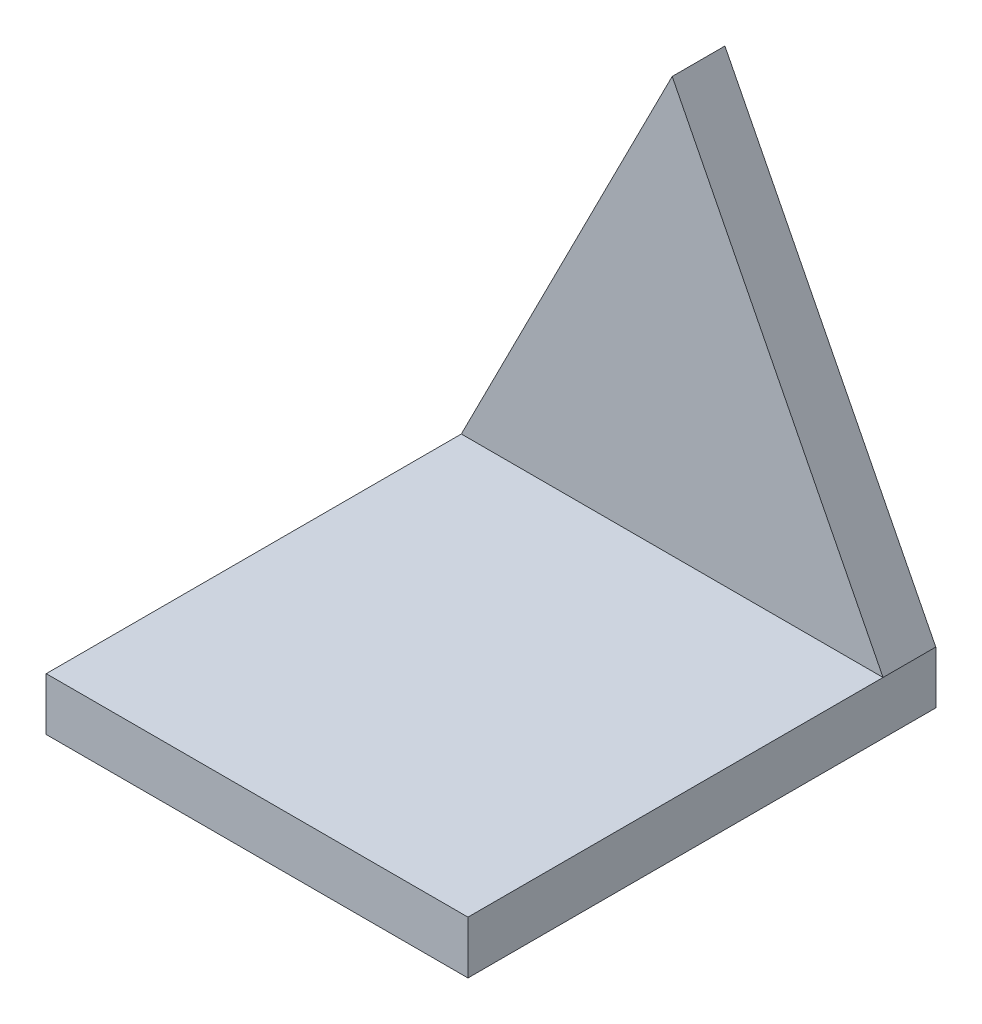
SolidWorks part; units mm, degrees
ref_plane "Front Plane" through (0, 0, 0) normal (0, 0, 1) x (1, 0, 0)
ref_plane "Top Plane" through (0, 0, 0) normal (0, 1, 0) x (1, 0, 0)
ref_plane "Right Plane" through (0, 0, 0) normal (1, 0, 0) x (0, 0, -1)
sketch "Sketch2" plane through (0, 0, 0) normal (0, 1, 0) x (1, 0, 0)
  line L1 (0, 0) -> (25.4, 0)
  line L2 (0, 0) -> (0, 28.175)
  line L3 (0, 28.175) -> (25.4, 28.175)
  line L4 (25.4, 0) -> (25.4, 28.175)
  dimension "D1" = 28.175
  dimension "D2" = 25.4
extrude "Boss-Extrude1" add sketch "Sketch2" along normal blind 3.175
sketch "Sketch3" plane through (0, 3.175, 0) normal (0, 1, 0) x (1, 0, 0)
  line L0 (25.4, 0) -> (25.4, 28.175) construction
  line L1 (0, 28.175) -> (25.4, 28.175)
  line L2 (0, 28.175) -> (0, 25)
  line L3 (0, 25) -> (25.4, 25)
  line L4 (25.4, 28.175) -> (25.4, 25)
  dimension "D1" = 3.175
extrude "Boss-Extrude2" add sketch "Sketch3" along normal blind 25
sketch "Sketch4" plane through (0, 0, -25) normal (0, 0, 1) x (1, 0, 0)
  line L0 (0, 3.175) -> (12.7, 28.175)
  line L1 (0, 28.175) -> (25.4, 28.175) construction
  line L2 (12.7, 28.175) -> (25.4, 3.175)
extrude "Cut-Extrude1" cut sketch "Sketch4" against normal through all and the other way through all
